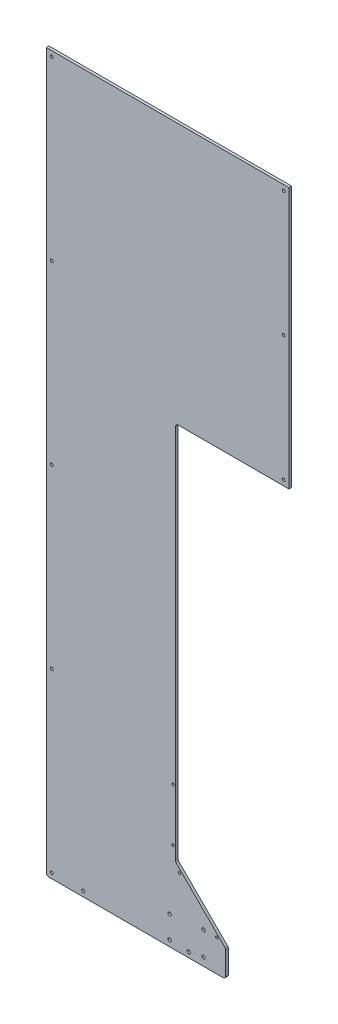
SolidWorks part; units mm, degrees
material "PC High Viscosity"
ref_plane "Front Plane" through (0, 0, 0) normal (0, 0, 1) x (1, 0, 0)
ref_plane "Top Plane" through (0, 0, 0) normal (0, 1, 0) x (1, 0, 0)
ref_plane "Right Plane" through (0, 0, 0) normal (1, 0, 0) x (0, 0, -1)
sketch "Sketch2" plane through (0, 0, 0) normal (0, 0, 1) x (1, 0, 0)
  line L1 (0, 0) -> (584.2, 0)
  line L2 (0, 0) -> (0, 1727.2)
  line L3 (0, 1727.2) -> (584.2, 1727.2)
  line L4 (584.2, 0) -> (584.2, 1727.2)
  dimension "D1" = 584.2
  dimension "D2" = 1727.2
extrude "Boss-Extrude1" add sketch "Sketch2" along normal blind 6.35
sketch "Sketch3" plane through (0, 0, 6.35) normal (0, 0, 1) x (1, 0, 0)
  line L0 (584.2, 1098.55) -> (311.15, 1098.55)
  line L1 (584.2, 0) -> (584.2, 1727.2) construction
  line L2 (311.15, 1098.55) -> (311.15, 184.15)
  line L5 (431.8, 56.7648) -> (333.3633, 155.2015) construction
  line L6 (584.2, 0) -> (431.8, 0)
  line L7 (584.2, 0) -> (584.2, 1098.55)
  line L8 (584.2, 1727.2) -> (0, 1727.2) construction
  line L9 (0, 1727.2) -> (0, 0) construction
  line L10 (311.15, 184.15) -> (431.8, 63.5)
  line L11 (431.8, 63.5) -> (431.8, 0)
  circle A0 centre (584.2, 279.4) radius 241.3 construction
  dimension "D3" = 279.4
  dimension "D5" = 482.6
  dimension "D7" = 431.8
  dimension "D1" = 628.65
  dimension "D2" = 311.15
  dimension "D4" = 584.2
  dimension "D6" = 273.05
  dimension "D8" = 63.5
  dimension "D9" = 135
  dimension "D10" = 9.525
  dimension "D11" = 56.7648
  dimension "D12" = 170.6249
extrude "Cut-Extrude1" cut sketch "Sketch3" against normal through all
sketch "Sketch4" plane through (0, 0, 6.35) normal (0, 0, 1) x (1, 0, 0)
  line L0 (0, 1727.2) -> (0, 0) construction
  line L1 (584.2, 1098.55) -> (584.2, 1727.2) construction
  line L2 (584.2, 1727.2) -> (0, 1727.2) construction
  point P0 (12.7, 1714.5)
  point P1 (12.7, 1289.05)
  point P2 (12.7, 863.6)
  point P3 (12.7, 438.15)
  point P4 (12.7, 12.7)
  point P5 (571.5, 1111.25)
  point P6 (571.5, 1412.875)
  point P7 (571.5, 1714.5)
  dimension "D1" = 12.7
  dimension "D2" = 12.7
  dimension "D3" = 12.7
  dimension "D4" = 301.625
  dimension "D5" = 603.25
  dimension "D6" = 425.45
  dimension "D7" = 425.45
  dimension "D8" = 425.45
  dimension "D9" = 425.45
hole_wizard "H (0.266) Diameter Hole1" positions "Sketch5" profile "Sketch6" hole size "H" standard "ANSI Inch" end condition through all
sketch "Sketch5" plane through (0, 0, 6.35) normal (0, 0, 1) x (1, 0, 0)
  point P0 (12.7, 1714.5)
  point P3 (12.7, 1289.05)
  point P6 (12.7, 863.6)
  point P9 (12.7, 438.15)
  point P12 (12.7, 12.7)
  point P15 (571.5, 1111.25)
  point P18 (571.5, 1412.875)
  point P21 (571.5, 1714.5)
sketch "Sketch6" plane through (12.7, 1714.5, 6.35) normal (1, 0, 0) x (0, -1, 0)
  line L0 (0, 0) -> (0, 6.35)
  line L1 (0, 6.35) -> (3.3782, 6.35)
  line L2 (3.3782, 6.35) -> (3.3782, 0)
  line L5 (3.3782, 0) -> (0, 0)
  line L11 (0, -6.35) -> (0, 107.95) construction
  dimension "Thru Hole Dia." = 6.7564
  dimension "Thru Hole Depth" = 6.35
fillet "Fillet1" radius 6.35 5 edges at (311.15, 1098.55, 3.175) (431.8, 63.5, 3.175) (311.15, 184.15, 3.175) (0, 0, 3.175) (431.8, 0, 3.175)
sketch "Sketch7" plane through (0, 0, 6.35) normal (0, 0, 1) x (1, 0, 0)
  line L0 (6.35, 0) -> (425.45, 0) construction
  line L1 (0, 1727.2) -> (0, 6.35) construction
  circle A0 centre (88.9, 12.7) radius 3.9688
  circle A1 centre (342.9, 12.7) radius 3.9688
  dimension "D1" = 12.7
  dimension "D3" = 7.9375
  dimension "D2" = 254
  dimension "D4" = 88.9
extrude "Cut-Extrude2" cut sketch "Sketch7" against normal blind 12.7
sketch "Sketch8" plane through (0, 0, 0) normal (0, 0, 1) x (1, 0, 0)
  line L0 (311.15, 1092.2) -> (311.15, 186.7803) construction
  line L1 (6.35, 0) -> (425.45, 0) construction
  circle A0 centre (304.8, 342.9) radius 3.3655 construction
  circle A1 centre (304.8, 215.9) radius 3.3655 construction
  point P5 (304.8, 342.9)
  point P8 (304.8, 215.9)
  dimension "D1" = 6.35
  dimension "D2" = 6.731
  dimension "D3" = 127
  dimension "D4" = 215.9
sketch "Sketch10" plane through (0, 0, 0) normal (0, 0, 1) x (1, 0, 0)
  line L0 (320.3172, 166.0026) -> (410.1197, 76.2) construction
  line L2 (313.0099, 182.2901) -> (429.9401, 65.3599) construction
  line L3 (6.35, 0) -> (425.45, 0) construction
  circle A0 centre (320.3172, 166.0026) radius 3.3655 construction
  circle A1 centre (410.1197, 76.2) radius 3.3655 construction
  point P9 (410.1197, 76.2)
  point P10 (320.3172, 166.0026)
  dimension "D1" = 127
  dimension "D4" = 6.731
  dimension "D2" = 76.2
  dimension "D3" = 6.35
hole_wizard "CSK for #10 Flat Head Machine Screw1" positions "Sketch13" profile "Sketch14" countersink size "#10" standard "ANSI Inch" end condition through all
sketch "Sketch13" plane through (0, 0, 0) normal (0, 0, -1) x (-1, 0, 0)
  point P0 (-304.8, 342.9)
  point P3 (-304.8, 215.9)
  point P6 (-320.3172, 166.0026)
  point P9 (-410.1197, 76.2)
sketch "Sketch14" plane through (304.8, 342.9, 0) normal (1, 0, 0) x (0, 1, 0)
  line L0 (0, 0) -> (0, 6.35)
  line L1 (0, 6.35) -> (2.8067, 6.35)
  line L2 (2.8067, 6.35) -> (2.8067, 2.396)
  line L3 (2.8067, 2.396) -> (4.8895, 0)
  line L5 (4.8895, 0) -> (0, 0)
  line L6 (-2.8067, 2.396) -> (-4.8895, 0) construction
  line L11 (0, -6.35) -> (0, 107.95) construction
  dimension "Thru Hole Dia." = 5.6134
  dimension "Thru Hole Depth" = 6.35
  dimension "Near C'Sink Dia." = 9.779
  dimension "Near C'Sink Angle" = 82
sketch "Sketch15" plane through (0, 0, 6.35) normal (0, 0, 1) x (1, 0, 0)
  line L0 (431.8, 60.8697) -> (431.8, 6.35) construction
  line L1 (6.35, 0) -> (425.45, 0) construction
  circle A0 centre (378.4676, 19.05) radius 3.937
  circle A1 centre (378.4676, 76.2) radius 3.937
  dimension "D3" = 7.874
  dimension "D1" = 53.3324
  dimension "D2" = 57.15
  dimension "D4" = 19.05
extrude "Cut-Extrude3" cut sketch "Sketch15" against normal through all
hole_wizard "5/16 (0.3125) Diameter Hole1" positions "Sketch17" profile "Sketch18" hole size "5/16" standard "ANSI Inch" end condition through all
sketch "Sketch17" plane through (0, 0, 0) normal (0, 0, -1) x (-1, 0, 0)
  line L0 (-6.35, 0) -> (-425.45, 0) construction
  line L1 (0, 1727.2) -> (0, 6.35) construction
  point P0 (-296.8625, 68.2625)
  point P2 (-296.8625, 14.2875)
  point P9 (-304.8, 73.025)
  point P10 (0, 0)
  dimension "D1" = 53.975
  dimension "D2" = 14.2875
  dimension "D3" = 296.8625
sketch "Sketch18" plane through (296.8625, 68.2625, 0) normal (1, 0, 0) x (0, 1, 0)
  line L0 (0, 0) -> (0, 6.35)
  line L1 (0, 6.35) -> (3.9687, 6.35)
  line L2 (3.9687, 6.35) -> (3.9687, 0)
  line L5 (3.9687, 0) -> (0, 0)
  line L11 (0, -6.35) -> (0, 107.95) construction
  dimension "Thru Hole Dia." = 7.9375
  dimension "Thru Hole Depth" = 6.35
